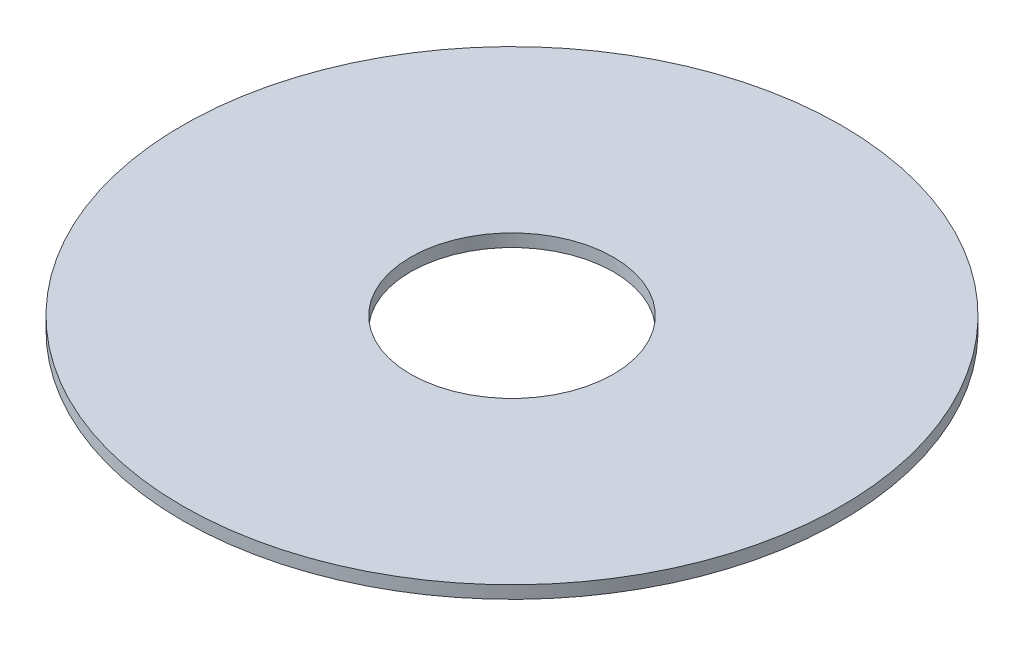
SolidWorks part; units mm, degrees
ref_plane "Front Plane" through (0, 0, 0) normal (0, 0, 1) x (1, 0, 0)
ref_plane "Top Plane" through (0, 0, 0) normal (0, 1, 0) x (1, 0, 0)
ref_plane "Right Plane" through (0, 0, 0) normal (1, 0, 0) x (0, 0, -1)
sketch "Sketch1" plane through (0, 0, 0) normal (0, 1, 0) x (1, 0, 0)
  circle A0 centre (0, 0) radius 6.5
  circle A1 centre (0, 0) radius 2
  dimension "D1" = 13
  dimension "D2" = 4
extrude "Boss-Extrude1" add sketch "Sketch1" along normal blind 0.25
